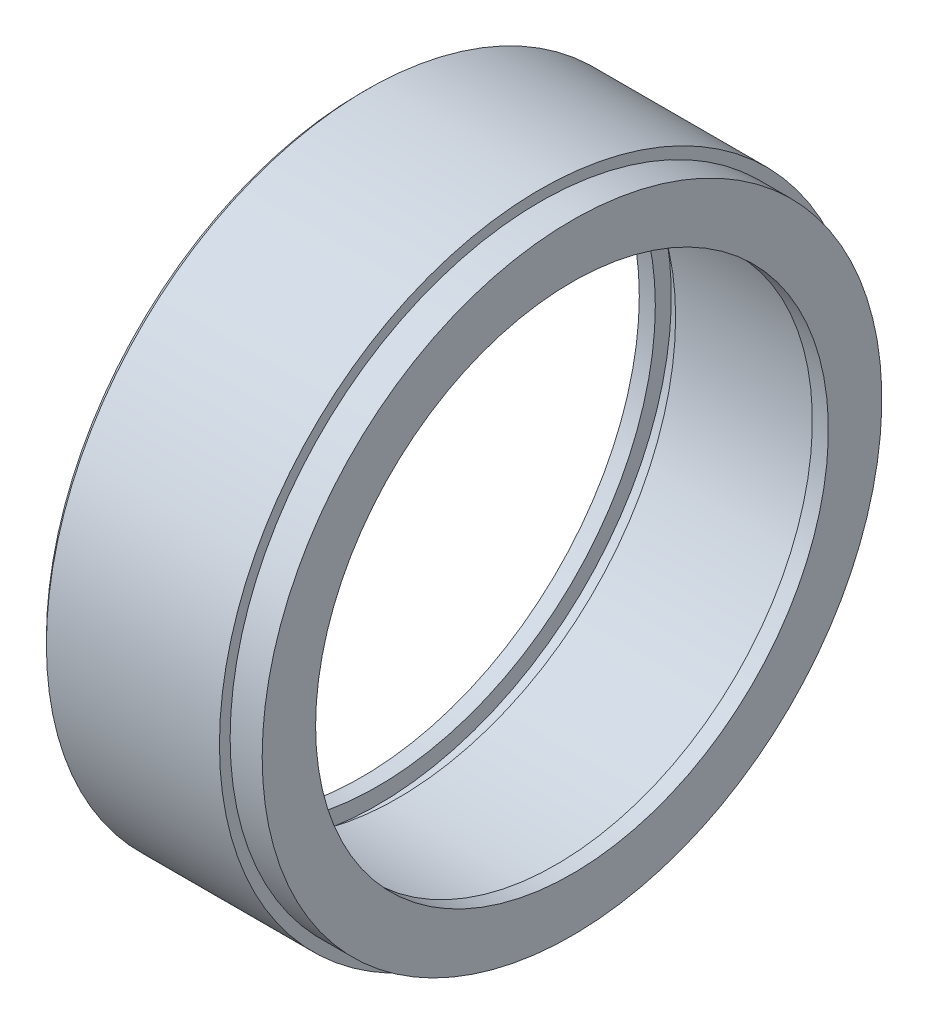
SolidWorks part; units mm, degrees
material "AISI 1020 Сталь, холоднокатаная"
ref_plane "Спереди" through (0, 0, 0) normal (0, 0, 1) x (1, 0, 0)
ref_plane "Сверху" through (0, 0, 0) normal (0, 1, 0) x (1, 0, 0)
ref_plane "Справа" through (0, 0, 0) normal (1, 0, 0) x (0, 0, -1)
sketch "Эскиз1" plane through (0, 0, 0) normal (0, 0, 1) x (1, 0, 0)
  line L0 (-1000, 0) -> (49000, 0) construction
  line L1 (0, 24) -> (-1.5, 24)
  line L2 (-1.5, 24) -> (-1.5, 26)
  line L3 (-1.5, 26) -> (-16.3, 26)
  line L4 (-19.7, 26) -> (-19.7, 30)
  line L5 (-19.7, 30) -> (-3, 30)
  line L6 (-3, 30) -> (-3, 29)
  line L7 (-3, 29) -> (0, 29)
  line L8 (0, 29) -> (0, 24)
  line L13 (-18.2, 26) -> (-19.7, 26)
  line L15 (-18.2, 26) -> (-18.2, 27.5)
  line L16 (-18.2, 27.5) -> (-16.3, 27.5)
  line L17 (-16.3, 26) -> (-16.3, 27.5)
  line L18 (-16.5, 27.5) -> (-16.5, 26) construction
  point P15 (-0.75, 24)
  dimension "D1" = 2
  dimension "D2" = 1
  dimension "D3" = 1.5
  dimension "D4" = 1.9
  dimension "D5" = 15
  dimension "D6" = 1.7
  dimension "D7" = 3
  dimension "D8" = 1.5
  dimension "D9" = 52
  dimension "D10" = 60
  dimension "D11" = 55
revolve "Повернуть1" add sketch "Эскиз1" angle 360 about L0
chamfer "Фаска1" distance 0.5 angle 45 1 edges at (-19.7, 0, 30)
